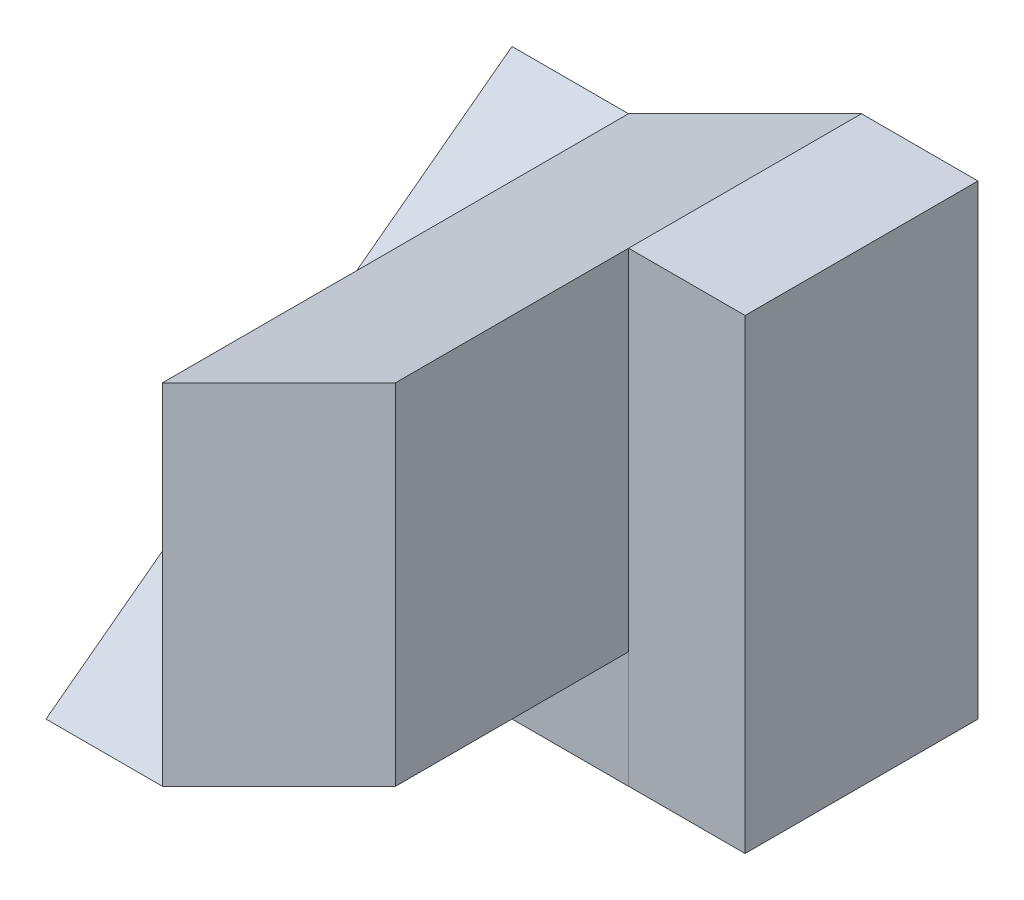
SolidWorks part; units mm, degrees
ref_plane "Front Plane" through (0, 0, 0) normal (0, 0, 1) x (1, 0, 0)
ref_plane "Top Plane" through (0, 0, 0) normal (0, 1, 0) x (1, 0, 0)
ref_plane "Right Plane" through (0, 0, 0) normal (1, 0, 0) x (0, 0, -1)
sketch "Sketch2" plane through (0, 0, 0) normal (1, 0, 0) x (0, 0, -1)
  line L0 (0, 0) -> (0, 3)
  line L1 (0, 3) -> (-4, 0)
  line L2 (-4, 0) -> (0, 0)
  dimension "D1" = 3
  dimension "D2" = 4
extrude "Boss-Extrude1" add sketch "Sketch2" along normal blind 1
sketch "Sketch3" plane through (1, 0, 0) normal (1, 0, 0) x (0, 0, -1)
  line L1 (-4, 0) -> (0, 0)
  line L2 (-4, 0) -> (-4, 4)
  line L3 (-4, 4) -> (0, 4)
  line L4 (0, 0) -> (0, 4)
  dimension "D1" = 4
  dimension "D2" = 4
extrude "Boss-Extrude2" add sketch "Sketch3" along normal blind 2
sketch "Sketch5" plane through (0, 0, 4) normal (0, 0, 1) x (1, 0, 0)
  line L0 (3, 4) -> (1, 3)
  line L1 (1, 4) -> (1, 0) construction
  line L2 (1, 3) -> (1, 4)
  line L3 (1, 4) -> (3, 4)
  line L4 (1, 0) -> (3, 1)
  line L5 (3, 4) -> (3, 0) construction
  line L6 (3, 1) -> (3, 0)
  line L7 (3, 0) -> (1, 0)
  dimension "D1" = 1
  dimension "D2" = 1
extrude "Cut-Extrude1" cut sketch "Sketch5" against normal blind 2
sketch "Sketch6" plane through (0, 0, 2) normal (0, 0, 1) x (1, 0, 0)
  line L0 (3, 4) -> (1, 4)
  line L1 (1, 4) -> (1, 3)
  line L2 (1, 3) -> (3, 4)
extrude "Cut-Extrude2" cut sketch "Sketch6" against normal blind 2
sketch "Sketch7" plane through (3, 0, 0) normal (1, 0, 0) x (0, 0, -1)
  line L1 (0, 0) -> (-1.9992, 0)
  line L2 (0, 0) -> (0, 4)
  line L3 (0, 4) -> (-1.9992, 4)
  line L4 (-1.9992, 0) -> (-1.9992, 4)
  dimension "D1" = 4
  dimension "D2" = 1.9992
extrude "Boss-Extrude3" add sketch "Sketch7" along normal blind 1
